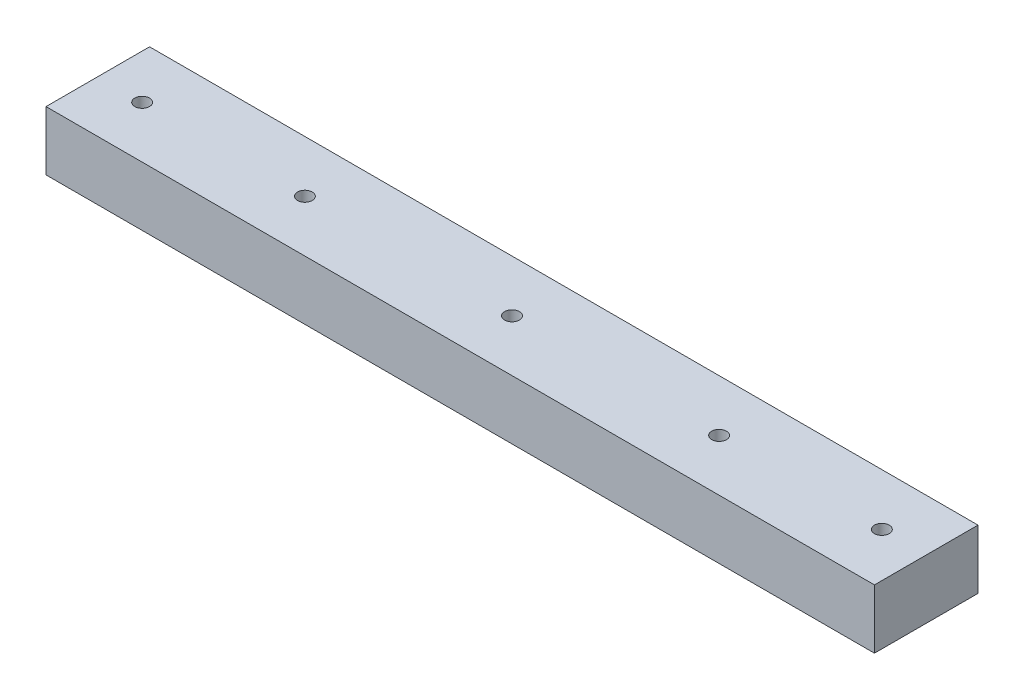
SolidWorks part; units mm, degrees
material "1023 Листовая углеродистая сталь (SS)"
ref_plane "Front" through (0, 0, 0) normal (0, 0, 1) x (1, 0, 0)
ref_plane "Top" through (0, 0, 0) normal (0, 1, 0) x (1, 0, 0)
ref_plane "Right" through (0, 0, 0) normal (1, 0, 0) x (0, 0, -1)
sketch "Sketch1" plane through (0, 0, 0) normal (0, 1, 0) x (1, 0, 0)
  line L1 (-140, 17.5) -> (140, 17.5)
  line L2 (-140, 17.5) -> (-140, -17.5)
  line L3 (-140, -17.5) -> (140, -17.5)
  line L4 (140, 17.5) -> (140, -17.5)
  line L5 (-140, 17.5) -> (140, -17.5) construction
  line L6 (-140, -17.5) -> (140, 17.5) construction
  point P0 (0, 0)
  dimension "D1" = 35
  dimension "D2" = 280
extrude "Extrude1" add sketch "Sketch1" along normal blind 20
hole_wizard "M6 Tapped Hole1" positions "Sketch2" profile "Sketch3" tap size "M6" standard "DIN"
sketch "Sketch2" plane through (0, 0, 0) normal (0, -1, 0) x (-1, 0, 0)
  point P0 (-125, 0)
  point P3 (-70, 0)
  point P6 (0, 0)
  point P9 (70, 0)
  point P12 (125, 0)
sketch "Sketch3" plane through (125, 0, 0) normal (1, 0, 0) x (0, 0, -1)
  line L0 (0, 0) -> (0, 30.5022)
  line L1 (0, 30.5022) -> (2.5, 29)
  line L2 (2.5, 29) -> (2.5, 0)
  line L5 (2.5, 0) -> (0, 0)
  line L10 (0, 30.5022) -> (-2.5, 29) construction
  line L11 (0, -6.35) -> (0, 107.95) construction
  dimension "Диаметр сверла" = 5
  dimension "Глубина сверла" = 29
  dimension "Угол заточки сверла" = 118
cosmetic thread "Cosmetic Thread1" parameters "D1"=24, "D2"=6
cosmetic thread "Cosmetic Thread2" parameters "D1"=24, "D2"=6
cosmetic thread "Cosmetic Thread3" parameters "D1"=24, "D2"=6
cosmetic thread "Cosmetic Thread4" parameters "D1"=24, "D2"=6
cosmetic thread "Cosmetic Thread5" parameters "D1"=24, "D2"=6
